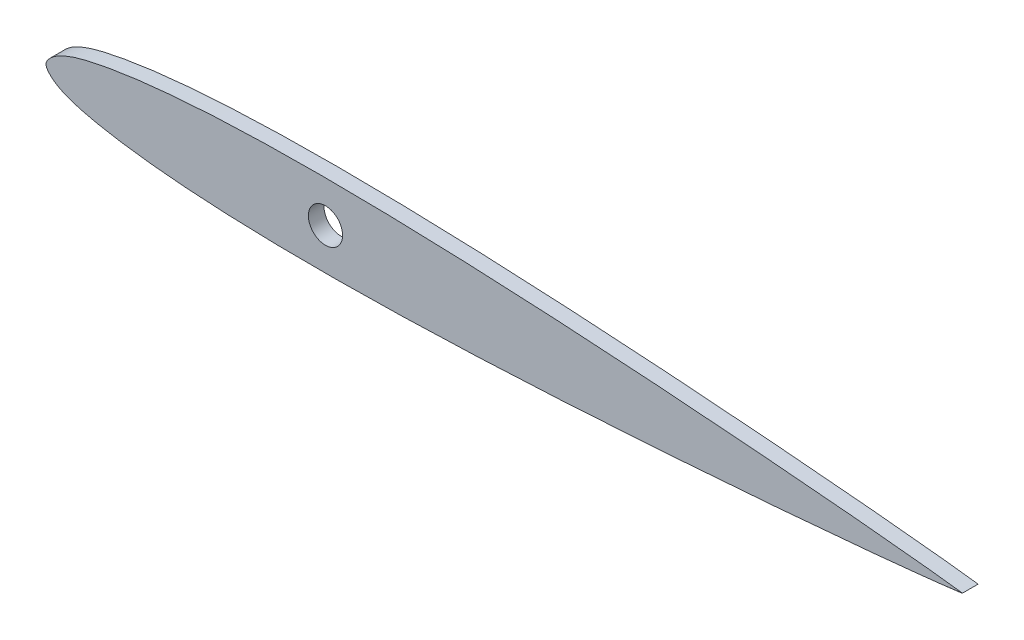
SolidWorks part; units mm, degrees
material "Balsa"
ref_plane "Front Plane" through (0, 0, 0) normal (0, 0, 1) x (1, 0, 0)
ref_plane "Top Plane" through (0, 0, 0) normal (0, 1, 0) x (1, 0, 0)
ref_plane "Right Plane" through (0, 0, 0) normal (1, 0, 0) x (0, 0, -1)
sketch "Sketch5" plane through (0, 0, 0) normal (0, 0, 1) x (1, 0, 0)
  spline S1 degree 3 poles (132.6352, -0.1273) (134.1653, 0) (132.6352, 0.1273) (131.3812, 0.3396) (128.335, 0.6651) (124.5922, 1.0691) (119.7155, 1.5433) (113.99, 2.0665) (107.4406, 2.6287) (100.2046, 3.2135) (92.3972, 3.7974) (84.1546, 4.3633) (75.6172, 4.885) (66.9312, 5.3404) (58.2449, 5.7025) (51.0726, 5.9117) (45.4464, 6.0078) (41.3533, 6.0419) (37.3694, 6.0372) (33.5118, 5.9859) (29.7974, 5.8959) (26.2422, 5.7599) (22.8612, 5.583) (19.6686, 5.361) (16.6778, 5.0976) (13.9025, 4.7906) (11.3544, 4.4458) (9.0435, 4.072) (6.9793, 3.671) (5.1685, 3.2442) (3.6198, 2.7772) (2.3364, 2.2613) (1.3302, 1.692) (0.6066, 1.0976) (0.1547, 0.5528) (-0.0633, 0) (0.1547, -0.5528) (0.6066, -1.0976) (1.3302, -1.692) (2.3364, -2.2613) (3.6198, -2.7772) (5.1685, -3.2442) (6.9793, -3.671) (9.0435, -4.072) (11.3544, -4.4458) (13.9025, -4.7906) (16.6778, -5.0976) (19.6686, -5.361) (22.8612, -5.583) (26.2422, -5.7599) (29.7974, -5.8959) (33.5118, -5.9859) (37.3694, -6.0372) (41.3533, -6.0419) (45.4464, -6.0078) (51.0726, -5.9117) (58.2449, -5.7025) (66.9312, -5.3404) (75.6172, -4.885) (84.1546, -4.3633) (92.3972, -3.7974) (100.2046, -3.2135) (107.4406, -2.6287) (113.99, -2.0665) (119.7155, -1.5433) (124.5922, -1.0691) (128.335, -0.6651) (131.3812, -0.3396) (132.6352, -0.1273) (134.1653, 0) (132.6352, 0.1273) knots -0.018944 -0.008488 -0.002133 0 0.002133 0.008488 0.018944 0.033319 0.051356 0.072756 0.097141 0.124097 0.153163 0.183834 0.215589 0.247878 0.280151 0.31186 0.327333 0.342463 0.357187 0.371448 0.385183 0.398331 0.410845 0.422673 0.433769 0.44409 0.453589 0.46224 0.47001 0.476871 0.482833 0.487909 0.492155 0.495592 0.498196 0.5 0.501804 0.504408 0.507845 0.512091 0.517167 0.523129 0.52999 0.53776 0.546411 0.55591 0.566231 0.577327 0.589155 0.601669 0.614817 0.628552 0.642813 0.657537 0.672667 0.68814 0.719849 0.752122 0.784411 0.816166 0.846837 0.875903 0.902859 0.927244 0.948644 0.966681 0.981056 0.991512 0.997867 1 1.002133 1.008488 1.018944 only from (133.858, 0) to (133.858, 0)
  dimension "D1" = 133.858
extrude "Boss-Extrude1" add sketch "Sketch5" along normal blind 2.286
sketch "Sketch6" plane through (0, 0, 2.286) normal (0, 0, 1) x (1, 0, 0)
  line L0 (0, 0) -> (40.8267, 0)
  circle A0 centre (40.8267, 0) radius 2.5
  dimension "D2" = 5
  dimension "D1" = 40.8267
extrude "Cut-Extrude1" cut sketch "Sketch6" against normal through all
